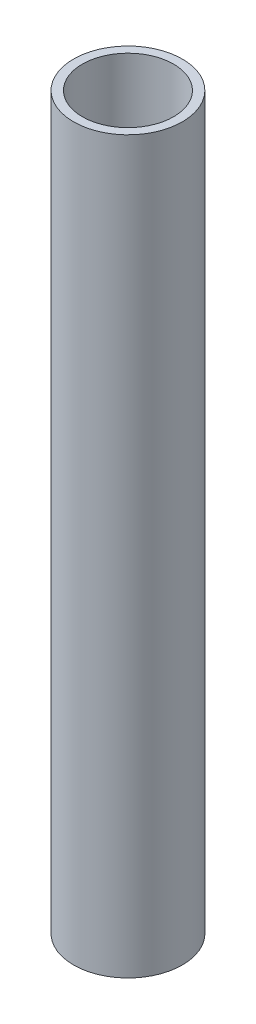
SolidWorks part; units mm, degrees
ref_plane "Front" through (0, 0, 0) normal (0, 0, 1) x (1, 0, 0)
ref_plane "Top" through (0, 0, 0) normal (0, 1, 0) x (1, 0, 0)
ref_plane "Right" through (0, 0, 0) normal (1, 0, 0) x (0, 0, -1)
sketch "Sketch1" plane through (0, 0, 0) normal (0, 1, 0) x (1, 0, 0)
  circle A0 centre (0, 0) radius 9.4615
  circle A1 centre (0, 0) radius 7.9375
  dimension "D1" = 18.923
  dimension "D2" = 15.875
extrude "Boss-Extrude1" add sketch "Sketch1" along normal mid plane 127
